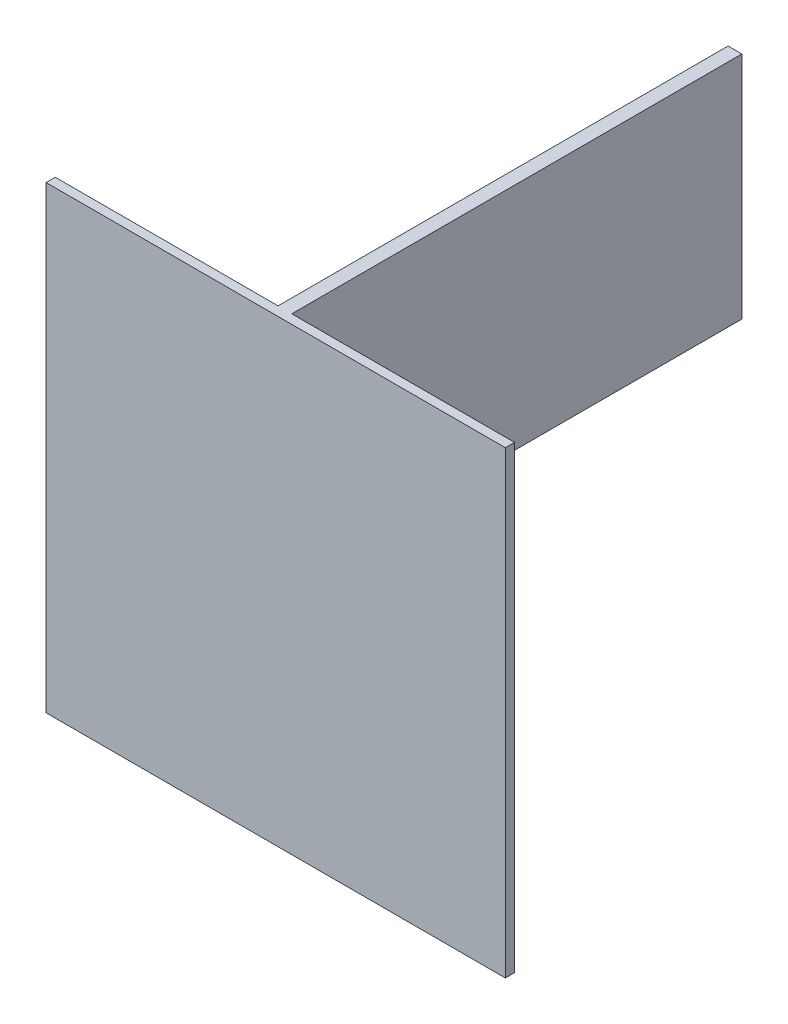
SolidWorks part; units mm, degrees
ref_plane "Płaszczyzna przednia" through (0, 0, 0) normal (0, 0, 1) x (1, 0, 0)
ref_plane "Płaszczyzna górna" through (0, 0, 0) normal (0, 1, 0) x (1, 0, 0)
ref_plane "Płaszczyzna prawa" through (0, 0, 0) normal (1, 0, 0) x (0, 0, -1)
sketch "Szkic1" plane through (0, 0, 0) normal (0, 0, 1) x (1, 0, 0)
  line L0 (0, 0) -> (100, 0)
  line L1 (0, 0) -> (-100, 0)
  line L2 (0, 0) -> (0, 100)
  line L3 (0, 0) -> (0, -100)
  line L4 (0, 100) -> (100, 100)
  line L5 (100, 100) -> (100, 0)
  line L6 (100, -100) -> (0, -100)
  line L7 (100, 0) -> (100, -100)
  line L8 (0, 100) -> (-100, 100)
  line L9 (-100, 100) -> (-100, 0)
  line L10 (-100, -100) -> (-100, 0)
  line L11 (0, -100) -> (-100, -100)
  dimension "D1" = 100
  dimension "D2" = 100
  dimension "D3" = 100
  dimension "D4" = 100
  dimension "D5" = 100
  dimension "D6" = 100
  dimension "D7" = 100
  dimension "D8" = 100
  dimension "D9" = 100
  dimension "D10" = 100
  dimension "D11" = 100
extrude "Dodanie-wyciągnięcie1" add sketch "Szkic1" along normal blind 4 contours L8 L9 L1 L2 | L5 L4 L2 L0 | L7 L0 L3 L6 | L11 L3 L1 L10
sketch "Szkic2" plane through (0, 0, 0) normal (0, 0, -1) x (-1, 0, 0)
  line L0 (0, 100) -> (0, 0)
  line L1 (-100, 100) -> (100, 100) construction
  line L2 (0, 0) -> (3, 0)
  line L3 (0, 0) -> (-3, 0)
  line L4 (3, 0) -> (3, 100)
  line L5 (-3, 0) -> (-3, 100)
  line L6 (-3, 100) -> (3, 100)
  dimension "D1" = 3
  dimension "D2" = 3
extrude "Dodanie-wyciągnięcie2" add sketch "Szkic2" along normal blind 196 contours L3 L5 L6 L4 L2
